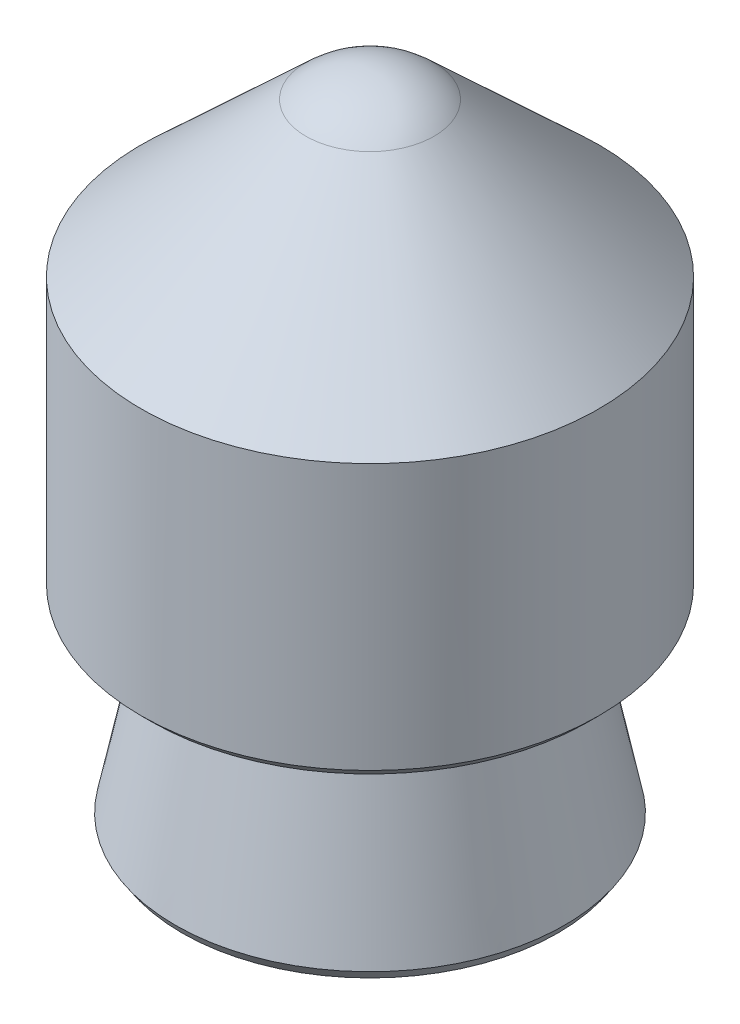
SolidWorks part; units mm, degrees
material "6061-T6 (SS)"
ref_plane "Front Plane" through (0, 0, 0) normal (0, 0, 1) x (1, 0, 0)
ref_plane "Top Plane" through (0, 0, 0) normal (0, 1, 0) x (1, 0, 0)
ref_plane "Right Plane" through (0, 0, 0) normal (1, 0, 0) x (0, 0, -1)
sketch "Sketch1" plane through (0, 0, 0) normal (0, 0, 1) x (1, 0, 0)
  line L0 (0, 25.4) -> (0, 41.3512) construction
  line L2 (4.7085, 14.7066) -> (-4.7085, 14.7066) construction
  line L3 (0, 25.4) -> (-4.8069, 25.4)
  line L4 (-3.8227, 30.2387) -> (-4.8069, 25.4)
  line L5 (0, 25.4) -> (0, 41.3512)
  line L6 (-3.8227, 30.2387) -> (-5.588, 30.2387)
  line L7 (-5.588, 30.2387) -> (-5.588, 36.9824)
  line L8 (-1.5634, 40.7354) -> (-5.588, 36.9824)
  arc A0 (-1.5634, 40.7354) -> (0, 41.3512) centre (0, 39.0588) cw
  dimension "D6" = 2.2923
  dimension "D1" = 26.6446
  dimension "D2" = 3.8227
  dimension "D3" = 11.176
  dimension "D4" = 6.7437
  dimension "D5" = 11.1125
  dimension "D7" = 4.8069
revolve "Revolve1" add sketch "Sketch1" angle 360 about L0
chamfer "Chamfer1" distance 0.254 angle 45 2 edges at (0, 25.4, -4.8069) (0, 30.2387, -5.588)
sketch "Sketch4" plane through (0, 25.4, 0) normal (0, -1, 0) x (1, 0, 0)
  circle A0 centre (0, 0) radius 3.5
  dimension "D1" = 7
extrude "Cut-Extrude1" cut sketch "Sketch4" against normal blind 2.5
hole_wizard "M7x0.75 Tapped Hole1" positions "Sketch5" profile "Sketch6" tap size "M7x1.0" standard "ANSI Metric"
sketch "Sketch5" plane through (0, 25.4, 0) normal (0, -1, 0) x (-1, 0, 0)
  point P0 (0, 0)
  point P3 (96.1394, -180.6847)
sketch "Sketch6" plane through (0, 25.4, 0) normal (1, 0, 0) x (0, 0, -1)
  line L0 (0, 0) -> (0, 12.7566)
  line L1 (0, 12.7566) -> (3, 10.954)
  line L2 (3, 10.954) -> (3, 0)
  line L5 (3, 0) -> (0, 0)
  line L10 (0, 12.7566) -> (-3, 10.954) construction
  line L11 (0, -6.35) -> (0, 107.95) construction
  dimension "Tap Drill Dia." = 6
  dimension "Tap Drill Depth" = 10.954
  dimension "Drill Angle" = 118
cosmetic thread "Hole Thread1"
